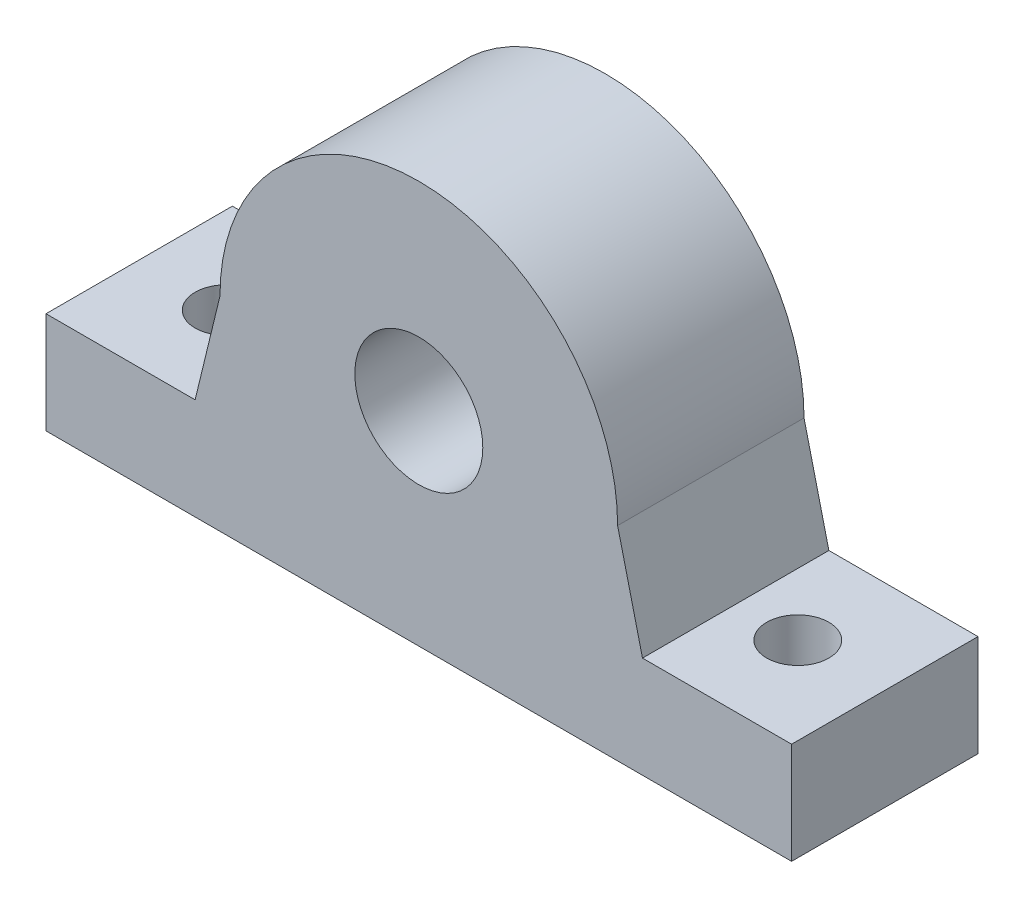
SolidWorks part; units mm, degrees
ref_plane "Front Plane" through (0, 0, 0) normal (0, 0, 1) x (1, 0, 0)
ref_plane "Top Plane" through (0, 0, 0) normal (0, 1, 0) x (1, 0, 0)
ref_plane "Right Plane" through (0, 0, 0) normal (1, 0, 0) x (0, 0, -1)
sketch "Sketch2" plane through (0, 0, 0) normal (0, 0, 1) x (1, 0, 0)
  line L0 (-16, 0) -> (-18, -8.2345)
  line L1 (-18, -8.2345) -> (-30, -8.2345)
  line L2 (-30, -8.2345) -> (-30, -16.4)
  line L3 (-30, -16.4) -> (30, -16.4)
  line L4 (0, 16) -> (0, -16.4) construction
  line L5 (30, -8.2345) -> (30, -16.4)
  line L6 (18, -8.2345) -> (30, -8.2345)
  line L7 (16, 0) -> (18, -8.2345)
  arc A0 (-16, 0) -> (16, 0) centre (0, 0) cw
  circle A1 centre (0, 0) radius 5.15
  dimension "D5" = 10.3
  dimension "D1" = 32
  dimension "D2" = 16.4
  dimension "D3" = 60
  dimension "D4" = 12
extrude "Boss-Extrude1" add sketch "Sketch2" along normal blind 15
sketch "Sketch3" plane through (0, 0, 0) normal (0, 0, 1) x (1, 0, 0)
  circle A0 centre (0, 0) radius 11
  dimension "D1" = 22
extrude "Cut-Extrude1" cut sketch "Sketch3" along normal blind 4
sketch "Sketch4" plane through (0, -8.2345, 0) normal (0, 1, 0) x (1, 0, 0)
  line L0 (0, 0) -> (0, -15) construction
  line L1 (-16, -15) -> (16, -15) construction
  line L2 (-30, -15) -> (-30, 0) construction
  line L3 (-18, 0) -> (-30, 0) construction
  circle A0 centre (-23, -7.5) radius 2.5
  circle A1 centre (23, -7.5) radius 2.5
  point P10 (-30, -7.5)
  point P14 (-24, 0)
  dimension "D1" = 5
  dimension "D2" = 46
extrude "Cut-Extrude2" cut sketch "Sketch4" against normal through all
